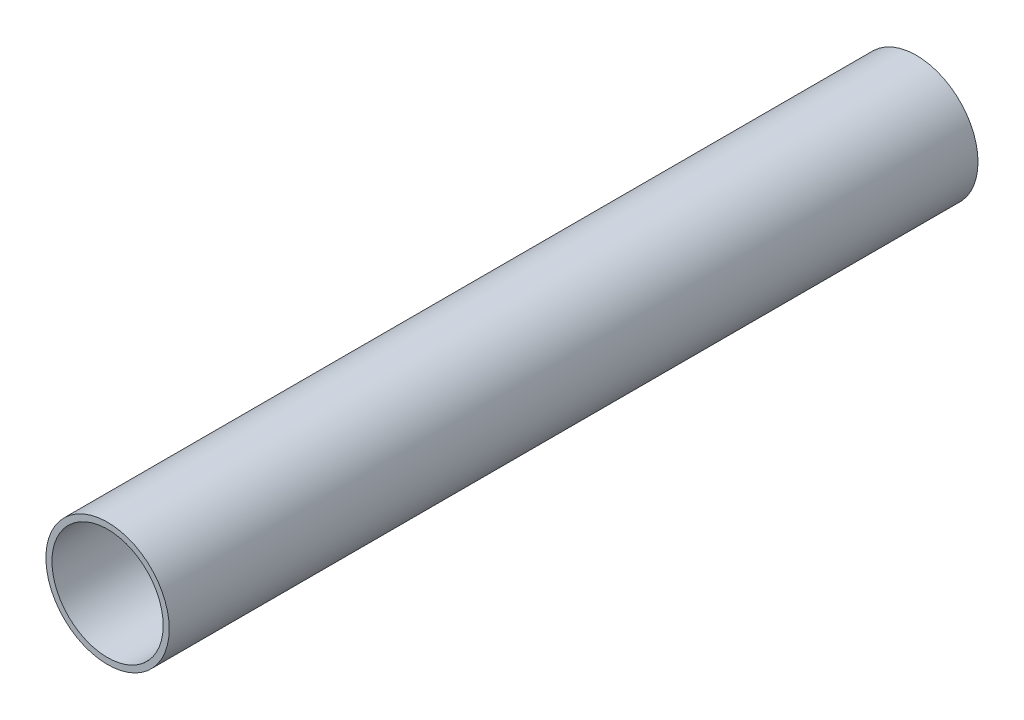
SolidWorks part; units mm, degrees
material "ABS"
ref_plane "Front Plane" through (0, 0, 0) normal (0, 0, 1) x (1, 0, 0)
ref_plane "Top Plane" through (0, 0, 0) normal (0, 1, 0) x (1, 0, 0)
ref_plane "Right Plane" through (0, 0, 0) normal (1, 0, 0) x (0, 0, -1)
sketch "Sketch1" plane through (0, 0, 0) normal (0, 0, 1) x (1, 0, 0)
  circle A0 centre (0, 0) radius 6.985
  circle A1 centre (0, 0) radius 7.747
  dimension "D1" = 13.97
  dimension "D2" = 15.494
extrude "Boss-Extrude1" add sketch "Sketch1" along normal blind 101.6
